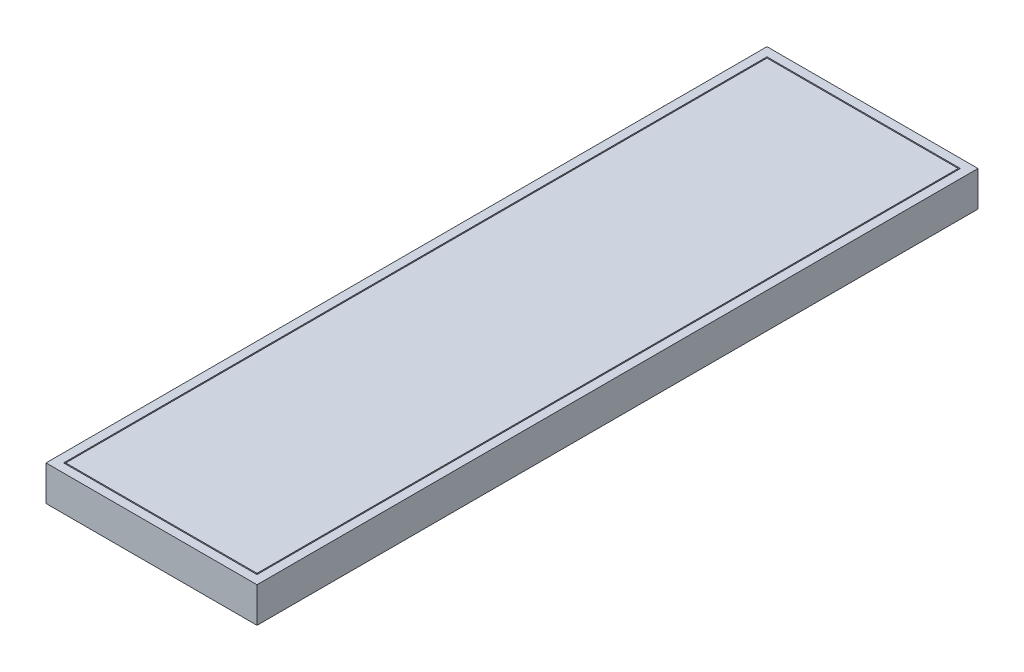
SolidWorks part; units mm, degrees
ref_plane "Front Plane" through (0, 0, 0) normal (0, 0, 1) x (1, 0, 0)
ref_plane "Top Plane" through (0, 0, 0) normal (0, 1, 0) x (1, 0, 0)
ref_plane "Right Plane" through (0, 0, 0) normal (1, 0, 0) x (0, 0, -1)
ref_plane "Plane1" through (0, -60, 0) normal (0, -1, 0) x (1, 0, 0)
sketch "Sketch1" plane through (0, -60, 0) normal (0, -1, 0) x (1, 0, 0)
  line L0 (-240, 0) -> (240, 0)
  line L1 (240, 0) -> (240, 1640)
  line L2 (240, 1640) -> (-240, 1640)
  line L3 (-240, 1640) -> (-240, 0)
  dimension "D1" = 1640
  dimension "D2" = 240
  dimension "D3" = 480
extrude "Boss-Extrude1" add sketch "Sketch1" against normal blind 80
sketch "Sketch2" plane through (0, 20, 0) normal (0, 1, 0) x (-1, 0, 0)
  line L0 (220, 1620) -> (-220, 1620)
  line L1 (-220, 1620) -> (-220, 20)
  line L2 (-220, 20) -> (220, 20)
  line L3 (220, 20) -> (220, 1620)
  dimension "D1" = 20
  dimension "D2" = 1600
  dimension "D3" = 220
  dimension "D4" = 440
extrude "Cut-Extrude1" cut sketch "Sketch2" against normal blind 11
sketch "Sketch3" plane through (0, 9, 0) normal (0, 1, 0) x (-1, 0, 0)
  line L0 (217.5, 1617.5) -> (217.5, 22.5)
  line L1 (217.5, 22.5) -> (-217.5, 22.5)
  line L2 (-217.5, 22.5) -> (-217.5, 1617.5)
  line L3 (-217.5, 1617.5) -> (217.5, 1617.5)
  line L4 (-220, 20) -> (220, 20) construction
  line L5 (220, 20) -> (220, 1620) construction
  dimension "D1" = 2.5
  dimension "D2" = 1595
  dimension "D3" = 2.5
  dimension "D4" = 435
extrude "Boss-Extrude2" add sketch "Sketch3" along normal blind 11
